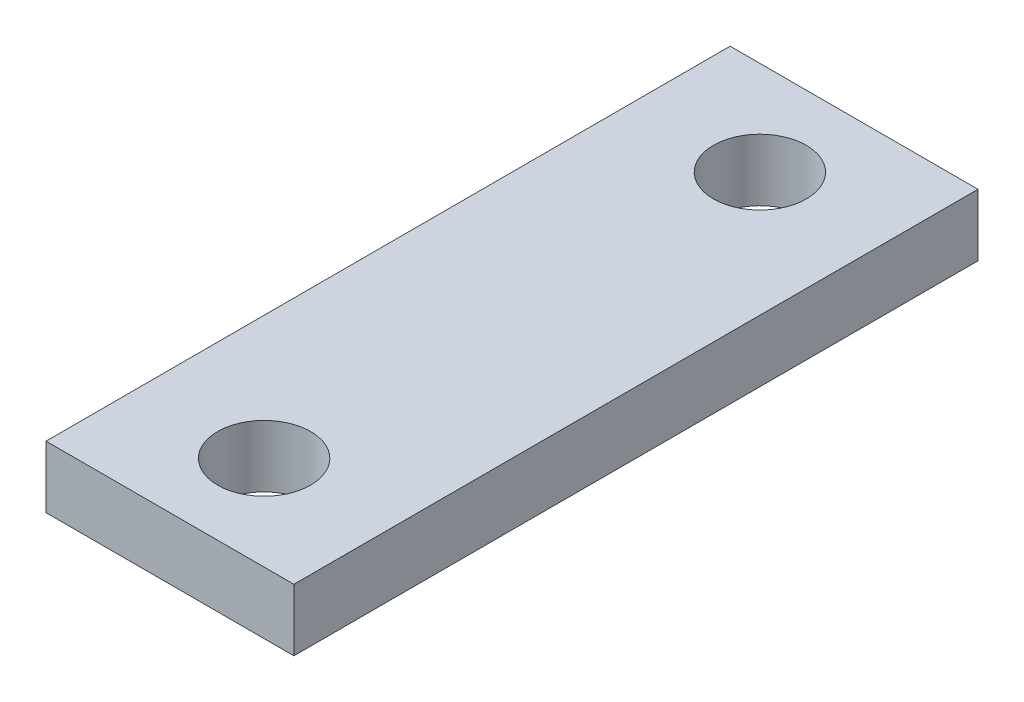
SolidWorks part; units mm, degrees
ref_plane "Front Plane" through (0, 0, 0) normal (0, 0, 1) x (1, 0, 0)
ref_plane "Top Plane" through (0, 0, 0) normal (0, 1, 0) x (1, 0, 0)
ref_plane "Right Plane" through (0, 0, 0) normal (1, 0, 0) x (0, 0, -1)
sketch "Sketch2" plane through (0, 0, 0) normal (0, 1, 0) x (1, 0, 0)
  line L0 (-12.7, 0) -> (12.7, 0) construction
  line L1 (-12.7, 35.052) -> (12.7, 35.052)
  line L2 (-12.7, 35.052) -> (-12.7, -35.052)
  line L3 (-12.7, -35.052) -> (12.7, -35.052)
  line L4 (12.7, 35.052) -> (12.7, -35.052)
  line L5 (0, 25.4) -> (0, -25.4)
  circle A0 centre (0, 25.4) radius 4.7625
  circle A1 centre (0, -25.4) radius 4.7625
  point P10 (0, 0)
  dimension "D3" = 9.525
  dimension "D1" = 25.4
  dimension "D2" = 70.104
  dimension "D4" = 50.8
extrude "Boss-Extrude1" add sketch "Sketch2" along normal blind 6.35
equation "\"Lead_Screw_Dist\" = 2in"
equation "\"Lead_Screw_Diam\" = 0.375in"
equation "\"D4@Sketch2\"=\"Lead_Screw_Dist\""
equation "\"D3@Sketch2\"=\"Lead_Screw_Diam\""
